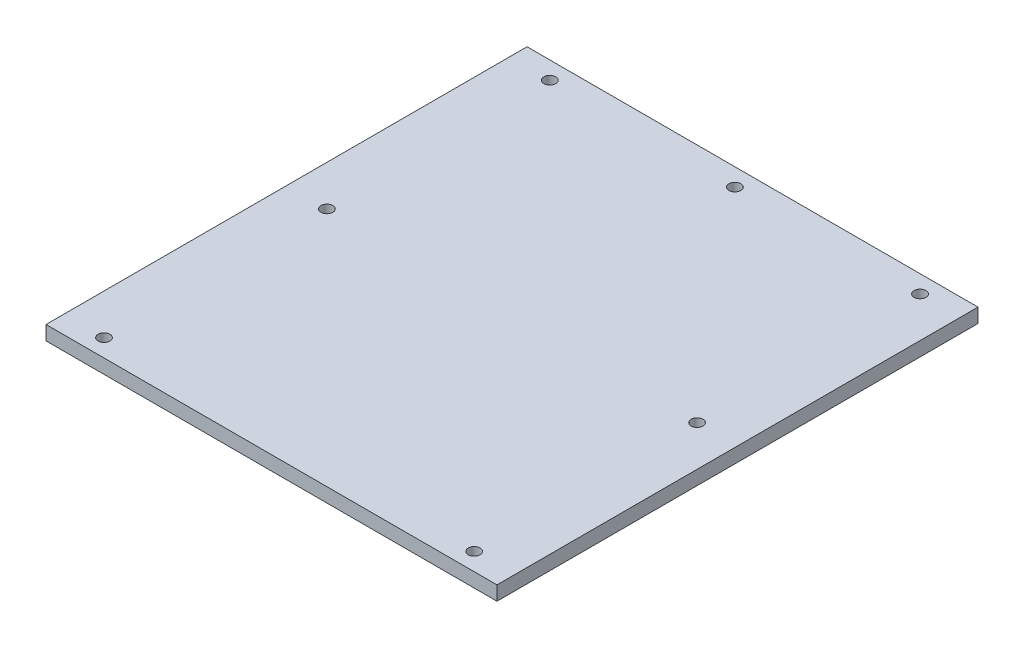
SolidWorks part; units mm, degrees
material "Acrylic (Medium-high impact)"
ref_plane "Front Plane" through (0, 0, 0) normal (0, 0, 1) x (1, 0, 0)
ref_plane "Top Plane" through (0, 0, 0) normal (0, 1, 0) x (1, 0, 0)
ref_plane "Right Plane" through (0, 0, 0) normal (1, 0, 0) x (0, 0, -1)
sketch "Sketch2" plane through (0, 0, 0) normal (0, 1, 0) x (1, 0, 0)
  line L1 (-95.25, 101.6) -> (95.25, 101.6)
  line L2 (-95.25, 101.6) -> (-95.25, -101.6)
  line L3 (-95.25, -101.6) -> (95.25, -101.6)
  line L4 (95.25, 101.6) -> (95.25, -101.6)
  line L5 (-95.25, 101.6) -> (95.25, -101.6) construction
  line L6 (-95.25, -101.6) -> (95.25, 101.6) construction
  point P0 (0, 0)
extrude "Boss-Extrude1" add sketch "Sketch2" along normal blind 6
sketch "Sketch5" plane through (0, 6, 0) normal (0, 1, 0) x (1, 0, 0)
  line L0 (-78.187, 101.6) -> (-78.187, 86.7301)
  line L1 (95.25, 101.6) -> (-95.25, 101.6) construction
  line L2 (-78.187, 94.1651) -> (-95.25, 94.1651)
  line L3 (-95.25, 101.6) -> (-95.25, -101.6) construction
  line L4 (0, 101.6) -> (0, -101.6)
  line L5 (-95.25, -101.6) -> (95.25, -101.6) construction
  line L6 (0, 0) -> (-95.25, 0)
  line L7 (0, 0) -> (95.25, 0)
  line L8 (95.25, -101.6) -> (95.25, 101.6) construction
  circle A0 centre (-78.187, 94.1651) radius 2.5
  circle A1 centre (78.187, 94.1651) radius 2.5
  circle A2 centre (-78.187, -94.1651) radius 2.5
  circle A3 centre (78.187, -94.1651) radius 2.5
  circle A4 centre (-78.187, 0) radius 2.5
  circle A5 centre (78.187, 0) radius 2.5
  circle A7 centre (0, 94.1651) radius 2.5
extrude "Cut-Extrude6" cut sketch "Sketch5" against normal through all
